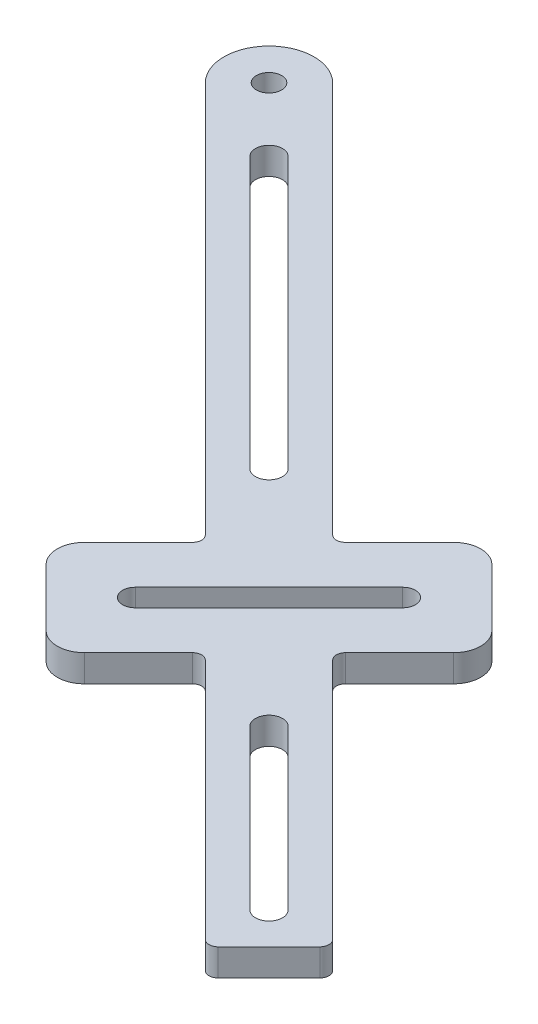
SolidWorks part; units mm, degrees
ref_plane "Front Plane" through (0, 0, 0) normal (0, 0, 1) x (1, 0, 0)
ref_plane "Top Plane" through (0, 0, 0) normal (0, 1, 0) x (1, 0, 0)
ref_plane "Right Plane" through (0, 0, 0) normal (1, 0, 0) x (0, 0, -1)
sketch "Sketch1" plane through (0, 0, 0) normal (0, 1, 0) x (1, 0, 0)
  line L16 (82.6259, -70.8778) -> (100.3035, -88.5555)
  line L17 (98.1822, -90.6768) -> (80.5045, -72.9992)
  line L18 (60.7763, -65.9988) -> (75.6255, -51.1496)
  line L19 (77.6054, -53.1295) -> (62.7562, -67.9787)
  line L20 (27.8251, -16.0771) -> (57.8771, -46.1291)
  line L21 (66.716, -50.0182) -> (23.2289, -6.5311)
  line L22 (16.1578, -13.6022) -> (59.6449, -57.0893)
  line L23 (59.6449, -58.5035) -> (53.6345, -64.5139)
  line L24 (53.6345, -68.7565) -> (59.9984, -75.1205)
  line L25 (64.2411, -75.1205) -> (70.2515, -69.1101)
  line L26 (71.6657, -69.1101) -> (98.5358, -95.9801)
  line L27 (99.95, -95.9801) -> (105.6068, -90.3233)
  line L28 (105.6068, -88.9091) -> (78.7368, -62.039)
  line L29 (78.7368, -60.6248) -> (84.7472, -54.6144)
  line L30 (84.7472, -50.3718) -> (78.3832, -44.0078)
  line L31 (74.1406, -44.0078) -> (68.1302, -50.0182)
  line L32 (55.7558, -48.2504) -> (25.7038, -18.1984)
  line L33 (26.7644, -17.1377) -> (99.2429, -89.6162) construction
  line L34 (76.6155, -52.1395) -> (61.7662, -66.9888) construction
  line L35 (75.6255, -51.1496) -> (77.6054, -53.1295) construction
  line L36 (60.7763, -65.9988) -> (62.7562, -67.9787) construction
  arc A45 (82.6259, -70.8778) -> (80.5045, -72.9992) centre (81.5652, -71.9385) ccw
  arc A46 (98.1822, -90.6768) -> (100.3035, -88.5555) centre (99.2429, -89.6162) ccw
  arc A47 (77.6054, -53.1295) -> (75.6255, -51.1496) centre (76.6155, -52.1395) ccw
  arc A48 (60.7763, -65.9988) -> (62.7562, -67.9787) centre (61.7662, -66.9888) ccw
  arc A49 (23.2289, -6.5311) -> (16.1578, -13.6022) centre (19.6934, -10.0667) ccw
  arc A50 (59.6449, -58.5035) -> (59.6449, -57.0893) centre (58.9378, -57.7964) ccw
  arc A51 (53.6345, -64.5139) -> (53.6345, -68.7565) centre (55.7558, -66.6352) ccw
  arc A52 (59.9984, -75.1205) -> (64.2411, -75.1205) centre (62.1198, -72.9992) ccw
  arc A53 (71.6657, -69.1101) -> (70.2515, -69.1101) centre (70.9586, -69.8172) ccw
  arc A54 (98.5358, -95.9801) -> (99.95, -95.9801) centre (99.2429, -95.273) ccw
  arc A55 (105.6068, -90.3233) -> (105.6068, -88.9091) centre (104.8997, -89.6162) ccw
  arc A56 (78.7368, -60.6248) -> (78.7368, -62.039) centre (79.4439, -61.3319) ccw
  arc A57 (84.7472, -54.6144) -> (84.7472, -50.3718) centre (82.6259, -52.4931) ccw
  arc A58 (78.3832, -44.0078) -> (74.1406, -44.0078) centre (76.2619, -46.1291) ccw
  arc A59 (66.716, -50.0182) -> (68.1302, -50.0182) centre (67.4231, -49.3111) ccw
  arc A60 (55.7558, -48.2504) -> (57.8771, -46.1291) centre (56.8165, -47.1898) ccw
  arc A61 (27.8251, -16.0771) -> (25.7038, -18.1984) centre (26.7644, -17.1377) ccw
  circle A62 centre (19.6934, -10.0667) radius 1.4
  point P1 (69.1908, -59.5641)
  point P2 (0, 0)
  dimension "D2" = 5
  dimension "D3" = 2.8
  dimension "D1" = 61.5
  dimension "D4" = 1.4
  dimension "D6" = 1.4
  dimension "D5" = 21
extrude "Boss-Extrude1" add sketch "Sketch1" along normal blind 3
